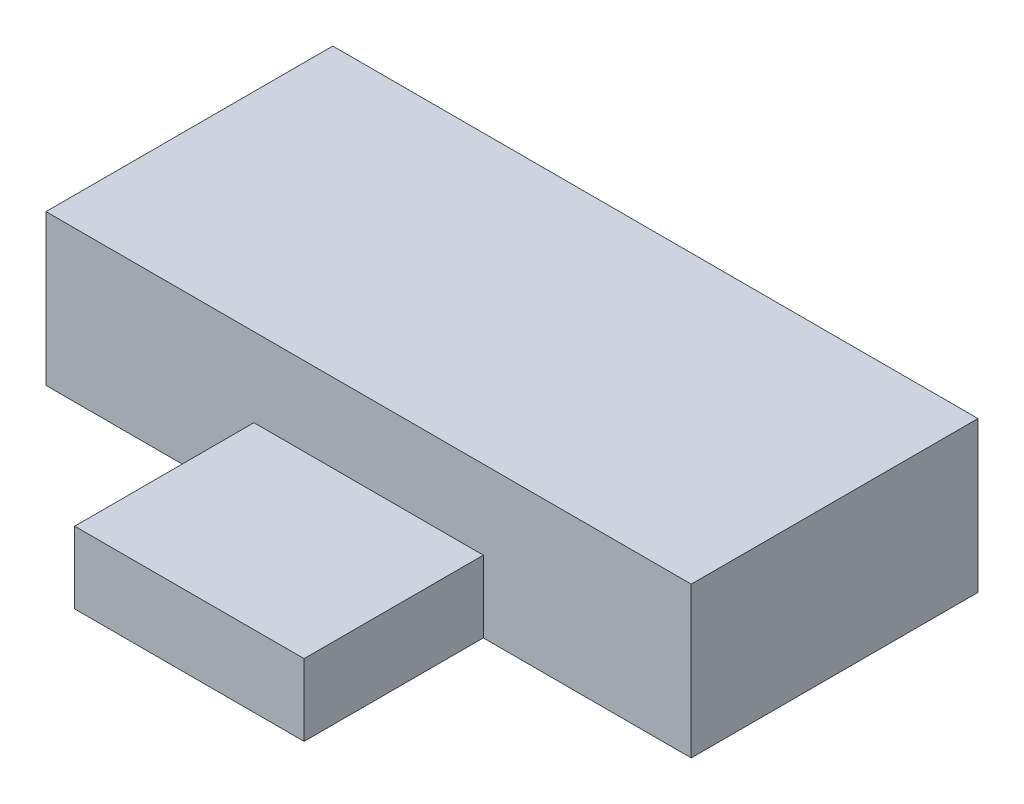
SolidWorks part; units mm, degrees
ref_plane "Plan de face" through (0, 0, 0) normal (0, 0, 1) x (1, 0, 0)
ref_plane "Plan de dessus" through (0, 0, 0) normal (0, 1, 0) x (1, 0, 0)
ref_plane "Plan de droite" through (0, 0, 0) normal (1, 0, 0) x (0, 0, -1)
sketch "Esquisse1" plane through (0, 0, 0) normal (0, 1, 0) x (1, 0, 0)
  line L1 (-9, 4) -> (9, 4)
  line L2 (-9, 4) -> (-9, -4)
  line L3 (-9, -4) -> (9, -4)
  line L4 (9, 4) -> (9, -4)
  line L5 (-9, 4) -> (9, -4) construction
  line L6 (-9, -4) -> (9, 4) construction
  point P0 (0, 0)
  dimension "D1" = 18
  dimension "D2" = 8
extrude "Boss.-Extru.1" add sketch "Esquisse1" along normal blind 4.2
sketch "Esquisse2" plane through (0, 0, 4) normal (0, 0, 1) x (1, 0, 0)
  line L0 (0, 1) -> (0, 0) construction
  line L1 (-3.2, 2) -> (3.2, 2)
  line L2 (-3.2, 2) -> (-3.2, 0)
  line L3 (-3.2, 0) -> (3.2, 0)
  line L4 (3.2, 2) -> (3.2, 0)
  line L5 (-3.2, 2) -> (3.2, 0) construction
  line L6 (-3.2, 0) -> (3.2, 2) construction
  line L7 (-9, 0) -> (9, 0) construction
  point P0 (0, 1)
  dimension "D1" = 2
  dimension "D2" = 6.4
extrude "Boss.-Extru.2" add sketch "Esquisse2" along normal blind 5
